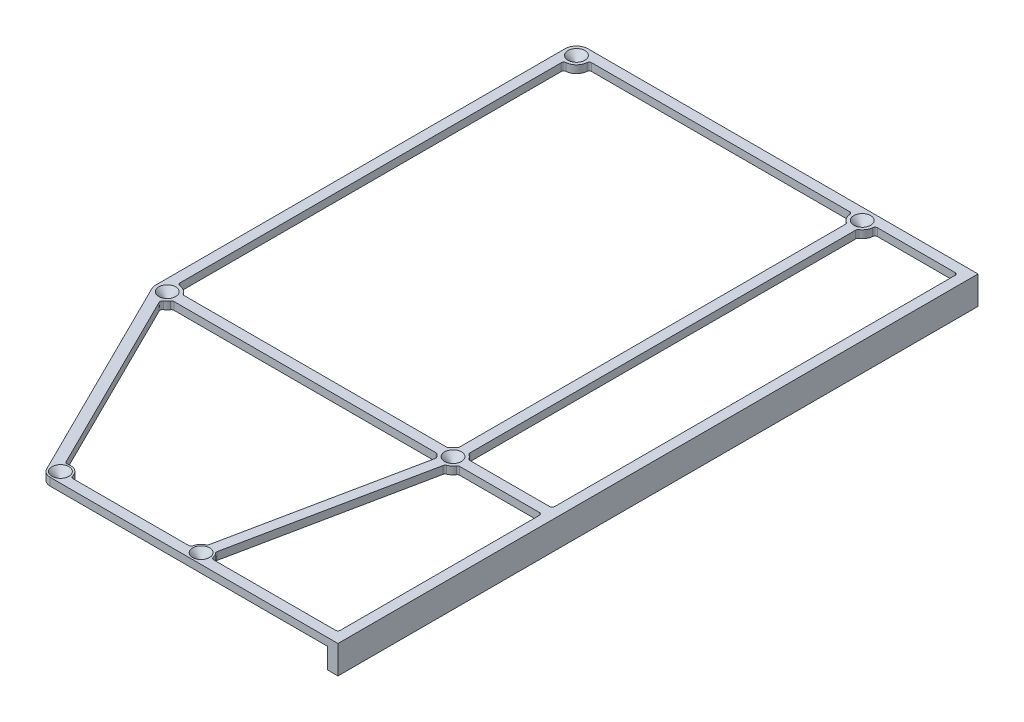
SolidWorks part; units mm, degrees
ref_plane "Front Plane" through (0, 0, 0) normal (0, 0, 1) x (1, 0, 0)
ref_plane "Top Plane" through (0, 0, 0) normal (0, 1, 0) x (1, 0, 0)
ref_plane "Right Plane" through (0, 0, 0) normal (1, 0, 0) x (0, 0, -1)
sketch "Sketch2" plane through (0, 0, 0) normal (0, 1, 0) x (1, 0, 0)
  line L0 (0, -4) -> (0, -162.5)
  line L2 (4, -250.2489) -> (4, 0)
  line L3 (4, 0) -> (0, 0)
  line L4 (-148.5, -4.5) -> (-148.5, 0.75) construction
  line L5 (-148.5, -4.5) -> (-36.75, -4.5) construction
  line L6 (-148.5, -4.5) -> (-148.5, -164.5) construction
  line L7 (-148.5, -164.5) -> (-36.75, -164.5) construction
  line L8 (-36.75, -4.5) -> (-36.75, -164.5) construction
  line L9 (-155.25, 0.75) -> (-30, 0.75) construction
  line L10 (-155.25, 0.75) -> (-155.25, -169.75) construction
  line L11 (-155.25, -169.75) -> (-30, -169.75) construction
  line L12 (-30, 0.75) -> (-30, -169.75) construction
  line L13 (-148.5, -4.5) -> (-155.25, -4.5) construction
  line L14 (-36.75, -164.5) -> (-36.75, -169.75) construction
  line L15 (-36.75, -164.5) -> (-30, -164.5) construction
  line L16 (-144.0279, -4) -> (-41.2221, -4)
  line L17 (-148.5, 0) -> (0, 0)
  line L18 (-32.2779, -4) -> (0, -4)
  line L19 (0, -4) -> (0, 0) construction
  line L20 (-32.2779, -4) -> (-36.2531, -4.4444) construction
  line L21 (-153, -4.5) -> (-153, -164.5)
  line L22 (-149, -8.9721) -> (-149, -160.0279)
  line L23 (-149, -8.9721) -> (-153, -8.9721) construction
  line L24 (-108.5, -246.25) -> (-53.5, -246.25) construction
  line L25 (-129, -204.75) -> (-30, -204.75) construction
  line L26 (-129, -204.75) -> (-129, -286.75) construction
  line L27 (-129, -286.75) -> (-30, -286.75) construction
  line L28 (-30, -204.75) -> (-30, -286.75) construction
  line L29 (-152.5311, -166.5) -> (-112.0823, -248.0273)
  line L30 (-108.5, -250.2489) -> (4, -250.2489)
  line L31 (-32.7189, -162.5) -> (0, -162.5)
  line L32 (-32.7189, -166.5) -> (0, -166.5)
  line L33 (-38.75, -8.5311) -> (-38.75, -160.4689)
  line L34 (-34.75, -8.5311) -> (-34.75, -160.4689)
  line L35 (-38.75, -8.5311) -> (-34.75, -8.5311) construction
  line L36 (-36.75, -164.5) -> (-53.5, -246.25) construction
  line L37 (-146.9603, -168.7284) -> (-110.2763, -242.6673)
  line L38 (-144.4689, -162.5) -> (-40.7811, -162.5)
  line L39 (-144.4689, -166.5) -> (-40.7811, -166.5)
  line L40 (-54.7642, -242.4562) -> (-39.5184, -168.0476)
  line L41 (-35.5998, -168.8505) -> (-50.8456, -243.2591)
  line L42 (-57.4989, -246.2489) -> (-104.5011, -246.2489)
  line L43 (-49.5011, -246.2489) -> (0, -246.2489)
  line L44 (-144.4689, -162.5) -> (-144.4689, -166.5) construction
  line L45 (-39.5184, -168.0476) -> (-35.5998, -168.8505) construction
  line L46 (-146.9603, -168.7284) -> (-150.5435, -170.5062) construction
  line L47 (-104.5011, -246.2489) -> (-104.5011, -250.2489) construction
  line L48 (0, -166.5) -> (0, -246.2489)
  circle A2 centre (-148.5, -4.5) radius 0.5
  circle A3 centre (-36.75, -4.5) radius 0.5
  circle A4 centre (-36.75, -164.5) radius 0.5
  circle A5 centre (-148.5, -164.5) radius 0.5
  arc A6 (-148.5, 0) -> (-153, -4.5) centre (-148.5, -4.5) ccw
  arc A7 (-41.2221, -4) -> (-38.75, -8.5311) centre (-36.75, -4.5) ccw
  arc A8 (-146.9603, -168.7284) -> (-144.4689, -166.5) centre (-148.5, -164.5) ccw
  arc A9 (-149, -8.9721) -> (-144.0279, -4) centre (-148.5, -4.5) ccw
  circle A10 centre (-108.5, -246.25) radius 0.5
  circle A11 centre (-53.5, -246.25) radius 0.5
  arc A12 (-112.0823, -248.0273) -> (-108.5, -250.2489) centre (-108.5, -246.25) ccw
  arc A14 (-40.7811, -166.5) -> (-39.5184, -168.0476) centre (-36.75, -164.5) ccw
  arc A15 (-34.75, -8.5311) -> (-32.2779, -4) centre (-36.75, -4.5) ccw
  arc A16 (-144.4689, -162.5) -> (-149, -160.0279) centre (-148.5, -164.5) ccw
  arc A17 (-57.4989, -246.2489) -> (-54.7642, -242.4562) centre (-53.5, -246.25) cw
  arc A18 (-49.5011, -246.2489) -> (-50.8456, -243.2591) centre (-53.5, -246.25) ccw
  arc A19 (-104.5011, -246.2489) -> (-110.2763, -242.6673) centre (-108.5, -246.25) ccw
  arc A20 (-38.75, -160.4689) -> (-40.7811, -162.5) centre (-36.75, -164.5) ccw
  arc A21 (-32.7189, -162.5) -> (-34.75, -160.4689) centre (-36.75, -164.5) ccw
  arc A22 (-35.5998, -168.8505) -> (-32.7189, -166.5) centre (-36.75, -164.5) ccw
  arc A23 (-153, -164.5) -> (-152.5311, -166.5) centre (-148.5, -164.5) ccw
  dimension "D1" = 1
  dimension "D8" = 55
  dimension "D2" = 111.75
  dimension "D3" = 160
  dimension "D4" = 125.25
  dimension "D5" = 170.5
  dimension "D6" = 4
  dimension "D7" = 30
  dimension "D9" = 99
  dimension "D10" = 82
  dimension "D11" = 40.5
  dimension "D12" = 20.5
  dimension "D13" = 35
extrude "Boss-Extrude1" add sketch "Sketch2" along normal blind 3
sketch "Sketch3" plane through (0, 0, 0) normal (0, -1, 0) x (1, 0, 0)
  line L1 (4, 250.2489) -> (0, 250.2489)
  line L2 (4, 250.2489) -> (4, 0)
  line L3 (4, 0) -> (0, 0)
  line L4 (0, 250.2489) -> (0, 0)
extrude "Boss-Extrude2" add sketch "Sketch3" along normal blind 8
chamfer "Chamfer1" distance 2.8 angle 45 6 edges at (-108.5, 3, 246.75) (-53.5, 3, 246.75) (-36.75, 3, 165) (-148.5, 3, 165) (-36.75, 3, 5) (-148.5, 3, 5)
fillet "Fillet1" radius 1 28 edges at (-144.4689, 1.5, 162.5) (-149, 1.5, 160.0279) (0, 1.5, 246.2489) (-57.4989, 1.5, 246.2489) (-54.7642, 1.5, 242.4562) (-49.5011, 1.5, 246.2489) (-50.8456, 1.5, 243.2591) (-104.5011, 1.5, 246.2489) (-110.2763, 1.5, 242.6673) (-146.9603, 1.5, 168.7284) (-144.4689, 1.5, 166.5) (-40.7811, 1.5, 166.5) (-39.5184, 1.5, 168.0476) (0, 1.5, 166.5) (-35.5998, 1.5, 168.8505) (-32.7189, 1.5, 166.5) (-40.7811, 1.5, 162.5) (-38.75, 1.5, 160.4689) (-32.7189, 1.5, 162.5) (-34.75, 1.5, 160.4689) (0, 1.5, 162.5) (0, 1.5, 4) (-34.75, 1.5, 8.5311) (-32.2779, 1.5, 4) (-38.75, 1.5, 8.5311) (-41.2221, 1.5, 4) (-149, 1.5, 8.9721) (-144.0279, 1.5, 4)
